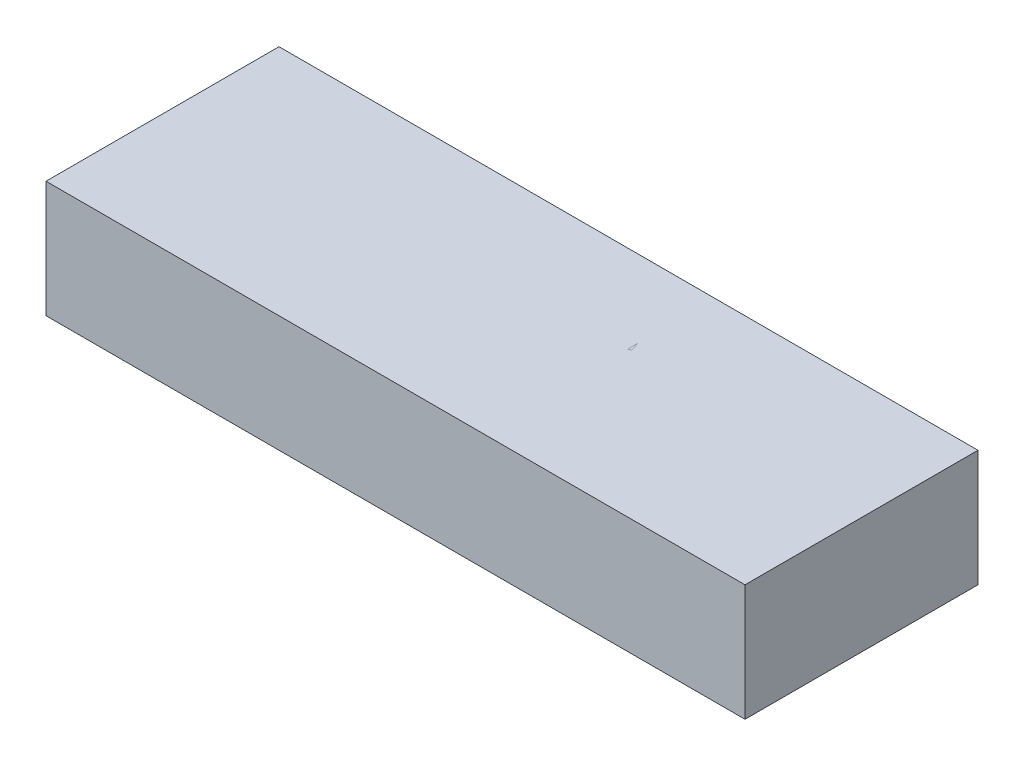
SolidWorks part; units mm, degrees
material "Acrylic (Medium-high impact)"
ref_plane "Front Plane" through (0, 0, 0) normal (0, 0, 1) x (1, 0, 0)
ref_plane "Top Plane" through (0, 0, 0) normal (0, 1, 0) x (1, 0, 0)
ref_plane "Right Plane" through (0, 0, 0) normal (1, 0, 0) x (0, 0, -1)
sketch "Sketch1" plane through (0, 0, 0) normal (0, 1, 0) x (1, 0, 0)
  line L1 (-19.05, -6.35) -> (19.05, -6.35)
  line L2 (-19.05, -6.35) -> (-19.05, 6.35)
  line L3 (-19.05, 6.35) -> (19.05, 6.35)
  line L4 (19.05, -6.35) -> (19.05, 6.35)
  line L5 (-19.05, -6.35) -> (19.05, 6.35) construction
  line L6 (-19.05, 6.35) -> (19.05, -6.35) construction
  point P0 (0, 0)
extrude "Boss-Extrude1" add sketch "Sketch1" along normal blind 6.35
sketch "Sketch2" plane through (0, 6.35, 0) normal (0, 1, 0) x (1, 0, 0)
  text T0 "<b>MOTOR 1</b>\r\n" font "Century Gothic" height in points 16
extrude "Boss-Extrude2" add sketch "Sketch2" against normal blind 0.508 separate body
